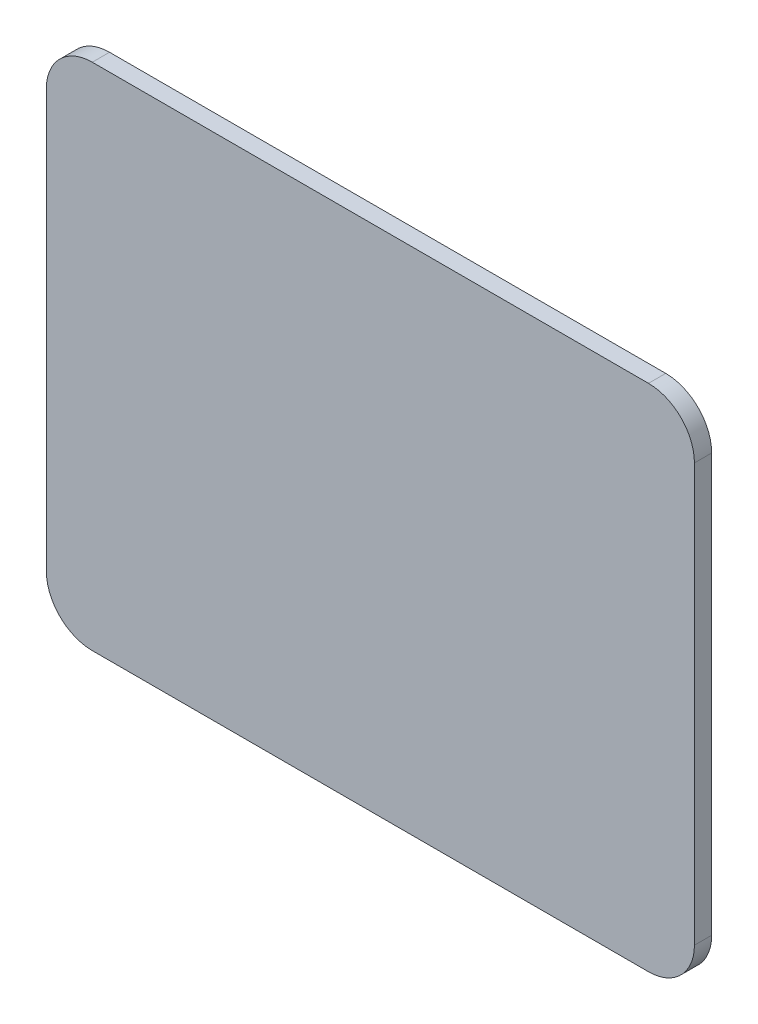
SolidWorks part; units mm, degrees
material "PC High Viscosity"
ref_plane "Front Plane" through (0, 0, 0) normal (0, 0, 1) x (1, 0, 0)
ref_plane "Top Plane" through (0, 0, 0) normal (0, 1, 0) x (1, 0, 0)
ref_plane "Right Plane" through (0, 0, 0) normal (1, 0, 0) x (0, 0, -1)
sketch "Sketch1" plane through (0, 0, 0) normal (0, 0, 1) x (1, 0, 0)
  line L4 (250.35, 26) -> (250.35, 171.4)
  line L5 (234.35, 187.4) -> (40.7313, 187.4)
  line L6 (24.7313, 171.4) -> (24.7313, 26)
  line L7 (40.7313, 10) -> (234.35, 10)
  line L8 (250.35, 26) -> (250.35, 171.4)
  line L9 (234.35, 187.4) -> (40.7313, 187.4)
  line L10 (24.7313, 171.4) -> (24.7313, 26)
  line L11 (40.7313, 10) -> (234.35, 10)
  arc A4 (250.35, 171.4) -> (234.35, 187.4) centre (234.35, 171.4) ccw
  arc A5 (40.7313, 187.4) -> (24.7313, 171.4) centre (40.7313, 171.4) ccw
  arc A6 (24.7313, 26) -> (40.7313, 10) centre (40.7313, 26) ccw
  arc A7 (234.35, 10) -> (250.35, 26) centre (234.35, 26) ccw
  arc A8 (250.35, 171.4) -> (234.35, 187.4) centre (234.35, 171.4) ccw
  arc A9 (40.7313, 187.4) -> (24.7313, 171.4) centre (40.7313, 171.4) ccw
  arc A10 (24.7313, 26) -> (40.7313, 10) centre (40.7313, 26) ccw
  arc A11 (234.35, 10) -> (250.35, 26) centre (234.35, 26) ccw
  dimension "D1" = 0
extrude "Boss-Extrude1" add sketch "Sketch1" along normal blind 6
